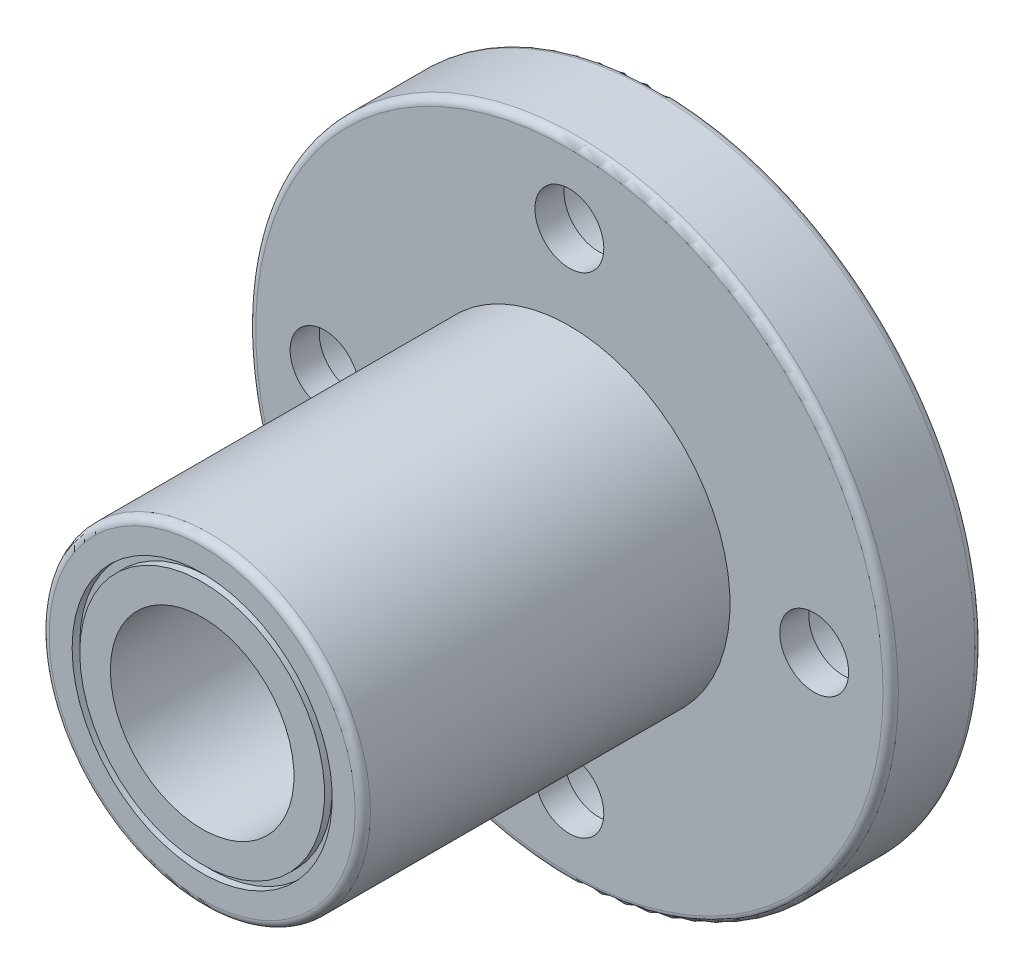
SolidWorks part; units mm, degrees
material "AISI 316 Отожженная нержавеющая сталь. полоса (SS)"
ref_plane "Plano frontal" through (0, 0, 0) normal (0, 0, 1) x (1, 0, 0)
ref_plane "Plano superior" through (0, 0, 0) normal (0, 1, 0) x (1, 0, 0)
ref_plane "Plano direito" through (0, 0, 0) normal (1, 0, 0) x (0, 0, -1)
sketch "Esboço1" plane through (0, 0, 0) normal (1, 0, 0) x (0, 0, -1)
  line L0 (0, 6) -> (0, 8)
  line L1 (0, 21) -> (-6, 21)
  line L2 (-6, 21) -> (-6, 10.5)
  line L3 (-6, 10.5) -> (-30, 10.5)
  line L4 (-30, 10.5) -> (-30, 8.5)
  line L5 (-30, 6) -> (0, 6)
  line L6 (0, 0) -> (-226.2321, 0) construction
  line L7 (-30, 8.5) -> (-29.5, 8.5)
  line L8 (-29.5, 8.5) -> (-29.5, 8)
  line L9 (-29.5, 8) -> (-30, 8)
  line L10 (0, 10.5) -> (-0.5, 10.5)
  line L11 (-0.5, 10.5) -> (-0.5, 10)
  line L12 (-0.5, 10) -> (0, 10)
  line L13 (0, 10.5) -> (0, 21)
  line L14 (-30, 8) -> (-30, 6)
  line L15 (0, 8.5) -> (-0.5, 8.5)
  line L16 (-0.5, 8.5) -> (-0.5, 8)
  line L17 (-0.5, 8) -> (0, 8)
  line L18 (0, 8.5) -> (0, 10)
  dimension "D1" = 30
  dimension "D2" = 21
  dimension "D3" = 12
  dimension "D4" = 42
  dimension "D5" = 6
  dimension "D6" = 0.5
  dimension "D7" = 0.5
  dimension "D8" = 0.5
  dimension "D9" = 0.5
  dimension "D10" = 0.5
  dimension "D11" = 0.5
revolve "Revolução1" add sketch "Esboço1" angle 360 about L6
sketch "Esboço5" plane through (0, 0, 0) normal (1, 0, 0) x (0, 0, -1)
  line L0 (0, 19.75) -> (-4.1, 19.75)
  line L1 (0, -21) -> (0, 21) construction
  line L2 (-4.1, 19.75) -> (-4.1, 18.25)
  line L3 (-4.1, 18.25) -> (-6, 18.25)
  line L4 (-6, 21) -> (-6, -21) construction
  line L5 (-6, 18.25) -> (-6, 16)
  line L6 (-6, 16) -> (0, 16)
  line L7 (0, 16) -> (0, 19.75)
  line L8 (0, 16) -> (2.2336, 16) construction
  line L9 (0, 0) -> (9.7959, 0) construction
  dimension "D1" = 7.5
  dimension "D2" = 4.5
  dimension "D3" = 4.1
  dimension "D4" = 32
revolve "Corte-Revolução1" cut sketch "Esboço5" angle 360 about L8
pattern_circular "PadrãoCircular1" count 4 over 360 about axis through (0, 0, 0) along (0, 0, 1) of "Corte-Revolução1"
fillet "Filete1" radius 0.5 3 edges at (-21, 0, 0) (-21, 0, 6) (-10.5, 0, 30)
